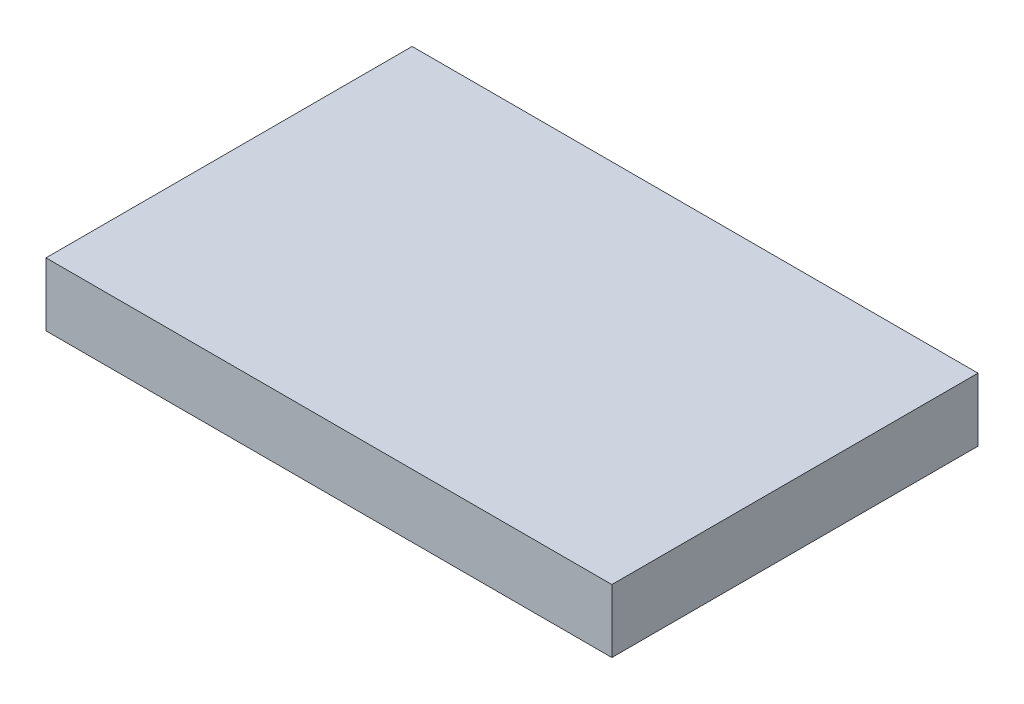
SolidWorks part; units mm, degrees
material "Ceramic Porcelain"
ref_plane "Front Plane" through (0, 0, 0) normal (0, 0, 1) x (1, 0, 0)
ref_plane "Top Plane" through (0, 0, 0) normal (0, 1, 0) x (1, 0, 0)
ref_plane "Right Plane" through (0, 0, 0) normal (1, 0, 0) x (0, 0, -1)
sketch "Sketch1" plane through (0, 0, 0) normal (0, 1, 0) x (1, 0, 0)
  line L1 (0, 0) -> (86.36, 0)
  line L2 (0, 0) -> (0, 55.88)
  line L3 (0, 55.88) -> (86.36, 55.88)
  line L4 (86.36, 0) -> (86.36, 55.88)
  dimension "D1" = 55.88
  dimension "D2" = 86.36
extrude "Boss-Extrude1" add sketch "Sketch1" along normal blind 9.652
